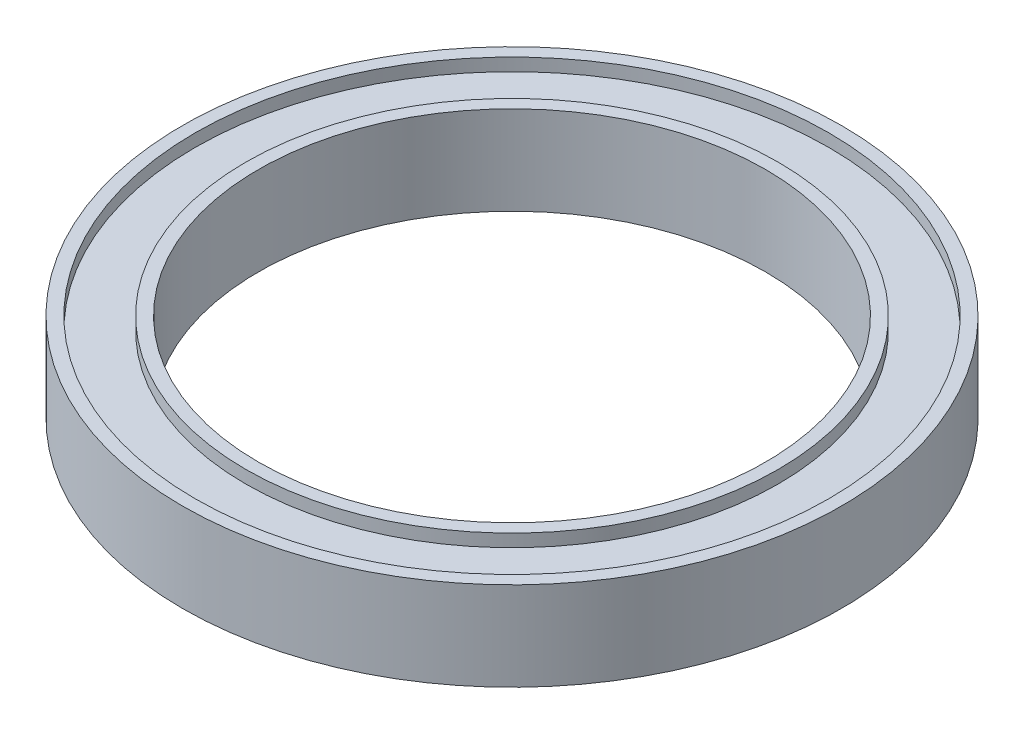
SolidWorks part; units mm, degrees
ref_plane "Alzado" through (0, 0, 0) normal (0, 0, 1) x (1, 0, 0)
ref_plane "Planta" through (0, 0, 0) normal (0, 1, 0) x (1, 0, 0)
ref_plane "Vista lateral" through (0, 0, 0) normal (1, 0, 0) x (0, 0, -1)
sketch "Croquis1" plane through (0, 0, 0) normal (0, 1, 0) x (1, 0, 0)
  circle A0 centre (0, 0) radius 20
  circle A1 centre (0, 0) radius 26
  dimension "D1" = 40
  dimension "D2" = 52
extrude "Saliente-Extruir1" add sketch "Croquis1" along normal mid plane 7
sketch "Croquis2" plane through (0, 3.5, 0) normal (0, 1, 0) x (1, 0, 0)
  circle A2 centre (0, 0) radius 25
  circle A5 centre (0, 0) radius 21
  circle A6 centre (0, 0) radius 20 construction
  circle A7 centre (0, 0) radius 26 construction
  dimension "D1" = 1
  dimension "D2" = 1
extrude "Cortar-Extruir1" cut sketch "Croquis2" against normal blind 1
mirror "Simetría1" about plane through (0, 0, 0) normal (0, 1, 0) of "Cortar-Extruir1"
